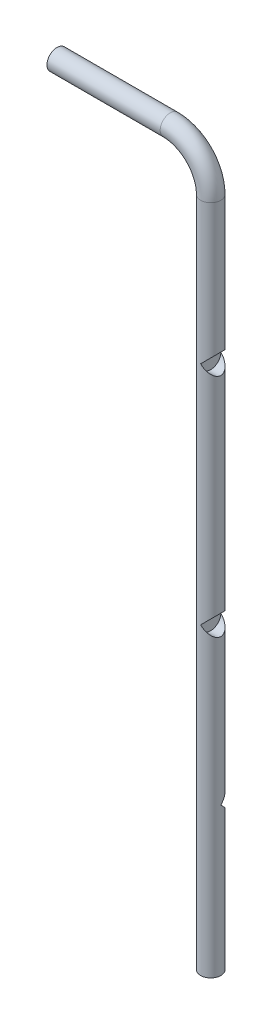
SolidWorks part; units mm, degrees
ref_plane "Front Plane" through (0, 0, 0) normal (0, 0, 1) x (1, 0, 0)
ref_plane "Top Plane" through (0, 0, 0) normal (0, 1, 0) x (1, 0, 0)
ref_plane "Right Plane" through (0, 0, 0) normal (1, 0, 0) x (0, 0, -1)
sketch "Sketch1" plane through (0, 0, 0) normal (0, 0, 1) x (1, 0, 0)
  line L0 (0, 0) -> (0, 830)
  line L1 (-50, 880) -> (-190, 880)
  arc A0 (0, 830) -> (-50, 880) centre (-50, 830) ccw
  dimension "D2" = 50
  dimension "D1" = 830
  dimension "D3" = 140
sweep "Sweep1" add path "Sketch1" circular profile diameter 25 parameters "D3"=25
sketch "Sketch2" plane through (0, 0, 0) normal (0, 0, 1) x (1, 0, 0)
  line L0 (0, 0) -> (0, 182.5) construction
  circle A0 centre (0, 182.5) radius 12.5
  dimension "D2" = 25
  dimension "D1" = 182.5
sketch "Sketch8" plane through (0, 0, 0) normal (1, 0, 0) x (0, 0, -1)
  line L0 (0, 830) -> (0, 655.01) construction
  line L1 (12.5, 830) -> (-12.5, 830) construction
  line L2 (0, 655.01) -> (0, 375.5) construction
  circle A0 centre (0, 655.01) radius 12.5
  circle A1 centre (0, 375.5) radius 12.5
  dimension "D2" = 25
  dimension "D4" = 25
  dimension "D1" = 174.99
  dimension "D3" = 279.51
extrude "Cut-Extrude3" cut sketch "Sketch8" along normal blind 21
extrude "Cut-Extrude5" cut sketch "Sketch2" against normal blind 13
